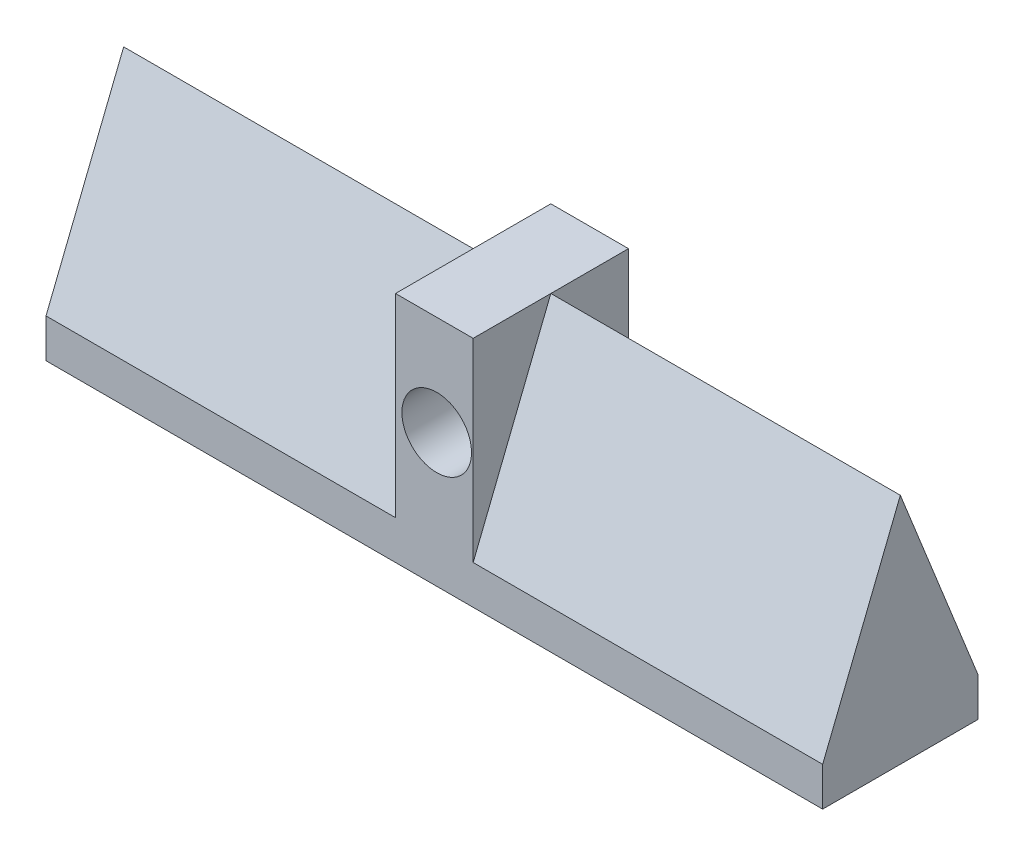
SolidWorks part; units mm, degrees
ref_plane "Front Plane" through (0, 0, 0) normal (0, 0, 1) x (1, 0, 0)
ref_plane "Top Plane" through (0, 0, 0) normal (0, 1, 0) x (1, 0, 0)
ref_plane "Right Plane" through (0, 0, 0) normal (1, 0, 0) x (0, 0, -1)
sketch "Sketch1" plane through (0, 0, 0) normal (1, 0, 0) x (0, 0, -1)
  line L0 (0, 0) -> (-200, 0)
  line L1 (-200, 0) -> (-200, 50)
  line L2 (0, 0) -> (0, 50)
  line L3 (-100, 0) -> (-100, 300) construction
  line L4 (-200, 50) -> (-100, 300)
  line L5 (0, 50) -> (-100, 300)
  dimension "D1" = 200
  dimension "D2" = 50
  dimension "D3" = 300
extrude "Boss-Extrude1" add sketch "Sketch1" along normal blind 1000
sketch "Sketch2" plane through (0, 0, 0) normal (0, 0, -1) x (-1, 0, 0)
  line L0 (-500, 50) -> (-500, 475.4778) construction
  line L1 (-1000, 50) -> (0, 50) construction
  line L2 (-550, 0) -> (-450, 0)
  line L4 (-1000, 0) -> (0, 0) construction
  line L5 (-450, 0) -> (-450, 300)
  line L6 (-1000, 300) -> (0, 300) construction
  line L7 (-450, 300) -> (-550, 300)
  line L8 (-550, 0) -> (-550, 300)
  point P13 (-500, 300)
  point P15 (-500, 0)
  dimension "D1" = 50
extrude "Boss-Extrude2" add sketch "Sketch2" against normal blind 200
sketch "Sketch3" plane through (0, 0, 0) normal (0, 0, -1) x (-1, 0, 0)
  circle A0 centre (-503.0811, 171.556) radius 44.8308
extrude "Cut-Extrude1" cut sketch "Sketch3" against normal through all both and the other way through all
